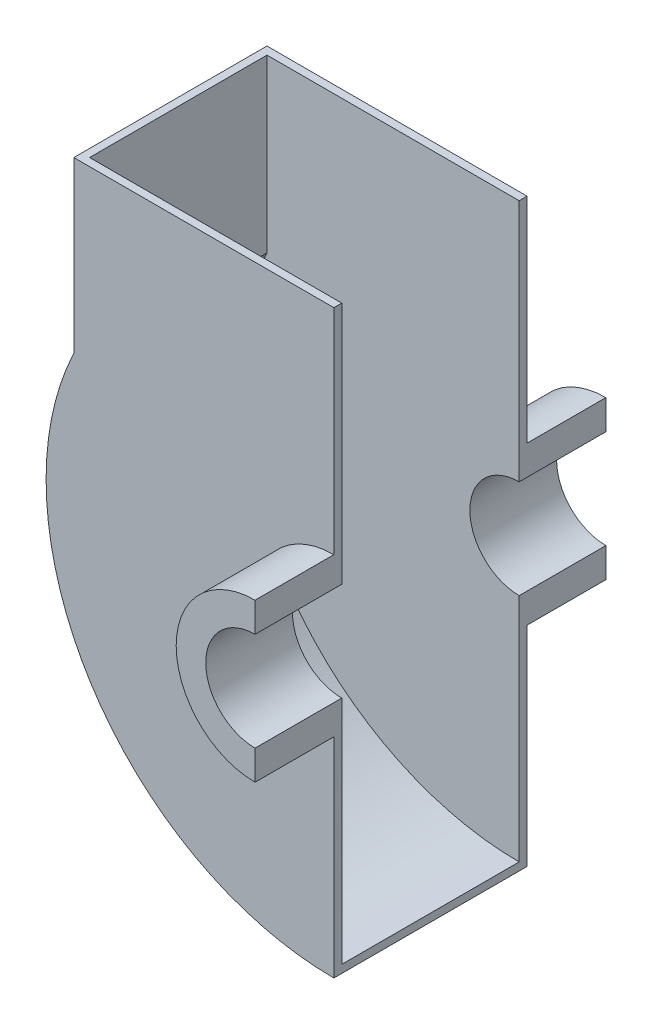
SolidWorks part; units mm, degrees
ref_plane "Ön Düzlem" through (0, 0, 0) normal (0, 0, 1) x (1, 0, 0)
ref_plane "Üst Düzlem" through (0, 0, 0) normal (0, 1, 0) x (1, 0, 0)
ref_plane "Sağ Düzlem" through (0, 0, 0) normal (1, 0, 0) x (0, 0, -1)
sketch "Sketch1" plane through (0, 0, 0) normal (0, 0, 1) x (1, 0, 0)
  line L0 (0, 0) -> (65.97, 0)
  line L1 (65.97, 0) -> (65.97, -61.7563)
  line L2 (65.97, -86.7563) -> (65.97, -147.2563)
  line L3 (0, 0) -> (0, -43)
  arc A0 (65.97, -61.7563) -> (65.97, -86.7563) centre (65.97, -74.2563) ccw
  arc A1 (65.97, -147.2563) -> (0, -43) centre (65.97, -74.2563) cw
  dimension "D3" = 12.5
  dimension "D4" = 73
  dimension "D1" = 65.97
  dimension "D2" = 43
extrude "Boss-Extrude1" add sketch "Sketch1" along normal mid plane 49
shell "Shell1" thickness 2
sketch "Sketch2" plane through (0, 0, 24.5) normal (0, 0, 1) x (1, 0, 0)
  line L0 (65.97, -54.2563) -> (65.97, -61.7563)
  line L1 (65.97, -86.7563) -> (65.97, -94.2563)
  arc A0 (65.97, -54.2563) -> (65.97, -94.2563) centre (65.97, -74.2563) ccw
  arc A1 (65.97, -61.7563) -> (65.97, -86.7563) centre (65.97, -74.2563) ccw
extrude "Boss-Extrude2" add sketch "Sketch2" along normal blind 20
mirror "Mirror1" about plane through (0, 0, 0) normal (0, 0, 1) of "Boss-Extrude2"
